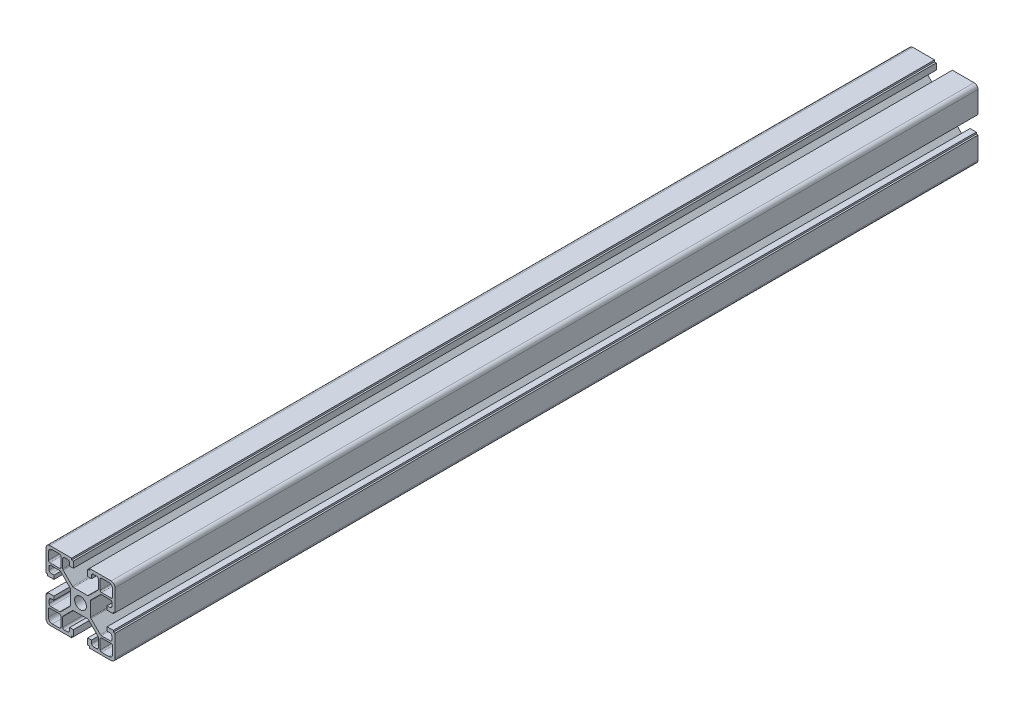
SolidWorks part; units mm, degrees
material "6063-T5"
ref_plane "Front Plane" through (0, 0, 0) normal (0, 0, 1) x (1, 0, 0)
ref_plane "Top Plane" through (0, 0, 0) normal (0, 1, 0) x (1, 0, 0)
ref_plane "Right Plane" through (0, 0, 0) normal (1, 0, 0) x (0, 0, -1)
sketch "Sketch1" plane through (0, 0, 0) normal (0, 0, 1) x (1, 0, 0)
  line L4 (20, 17.75) -> (20, 5.15)
  line L5 (0, -17.7813) -> (0, 18.2) construction
  line L6 (0, 0) -> (38.8613, 0) construction
  line L8 (18.6, 16.35) -> (18.6, 12.2)
  line L10 (11.4, 17.8) -> (11.4, 12.2)
  line L11 (-4.1, 5.85) -> (4.1, 5.85)
  line L14 (5.85, 4.1089) -> (5.85, -4.1089)
  line L17 (12.2, 11.4) -> (17.8, 11.4)
  line L24 (4.15, 19) -> (4.15, 15.4)
  line L25 (4.15, 15.4) -> (6.35, 15.4)
  line L26 (6.35, 15.4) -> (6.35, 16.95)
  line L27 (10.3, 17.2) -> (10.3, 12.0545)
  line L28 (10.0659, 11.489) -> (4.6659, 6.0845)
  line L29 (6.0841, 4.6743) -> (11.4708, 10.0655)
  line L30 (12.0367, 10.3) -> (17.2, 10.3)
  line L31 (18.2, 9.3) -> (18.2, 7.6)
  line L32 (16.95, 6.35) -> (15.4, 6.35)
  line L33 (15.4, 6.35) -> (15.4, 4.15)
  line L34 (15.4, 4.15) -> (19, 4.15)
  line L35 (18.6, 18.6) -> (18.6, -18.6) construction
  line L36 (-18.6, 18.6) -> (18.6, 18.6) construction
  line L37 (-20, 20) -> (20, 20) construction
  line L38 (20, 20) -> (20, -20) construction
  line L40 (7.6, 18.2) -> (9.3, 18.2)
  line L42 (4.15, 19) -> (5.15, 19)
  line L43 (5.15, 19) -> (5.15, 20)
  line L56 (-18.6, 18.6) -> (-18.6, -18.6) construction
  line L57 (-20, 20) -> (-20, -20) construction
  line L60 (5.15, 20) -> (17.75, 20)
  line L91 (-18.6, -18.6) -> (18.6, -18.6) construction
  line L92 (-20, -20) -> (20, -20) construction
  line L93 (12.2, 18.6) -> (16.35, 18.6)
  line L94 (17.9399, 17.9421) -> (20, 20) construction
  line L95 (0, 0) -> (11.4, 11.4094) construction
  line L101 (19, 4.15) -> (19, 5.15)
  line L102 (19, 5.15) -> (20, 5.15)
  line L104 (-5.85, 4.1089) -> (-5.85, -4.1089)
  line L105 (-19, 5.15) -> (-20, 5.15)
  line L106 (-19, 4.15) -> (-19, 5.15)
  line L107 (-12.2, 18.6) -> (-16.35, 18.6)
  line L108 (-5.15, 20) -> (-17.75, 20)
  line L109 (-5.15, 19) -> (-5.15, 20)
  line L110 (-4.15, 19) -> (-5.15, 19)
  line L111 (-7.6, 18.2) -> (-9.3, 18.2)
  line L112 (-15.4, 4.15) -> (-19, 4.15)
  line L113 (-15.4, 6.35) -> (-15.4, 4.15)
  line L114 (-16.95, 6.35) -> (-15.4, 6.35)
  line L115 (-18.2, 9.3) -> (-18.2, 7.6)
  line L116 (-12.0367, 10.3) -> (-17.2, 10.3)
  line L117 (-6.0841, 4.6743) -> (-11.4708, 10.0655)
  line L118 (-10.0659, 11.489) -> (-4.6659, 6.0845)
  line L119 (-10.3, 17.2) -> (-10.3, 12.0545)
  line L120 (-6.35, 15.4) -> (-6.35, 16.95)
  line L121 (-4.15, 15.4) -> (-6.35, 15.4)
  line L122 (-4.15, 19) -> (-4.15, 15.4)
  line L123 (-12.2, 11.4) -> (-17.8, 11.4)
  line L124 (-11.4, 17.8) -> (-11.4, 12.2)
  line L125 (-18.6, 16.35) -> (-18.6, 12.2)
  line L126 (-20, 17.75) -> (-20, 5.15)
  line L127 (-20, -17.75) -> (-20, -5.15)
  line L128 (-18.6, -16.35) -> (-18.6, -12.2)
  line L129 (-11.4, -17.8) -> (-11.4, -12.2)
  line L130 (-12.2, -11.4) -> (-17.8, -11.4)
  line L131 (-4.15, -19) -> (-4.15, -15.4)
  line L132 (-4.15, -15.4) -> (-6.35, -15.4)
  line L133 (-6.35, -15.4) -> (-6.35, -16.95)
  line L134 (-10.3, -17.2) -> (-10.3, -12.0545)
  line L135 (-10.0659, -11.489) -> (-4.6659, -6.0845)
  line L136 (-6.0841, -4.6743) -> (-11.4708, -10.0655)
  line L137 (-12.0367, -10.3) -> (-17.2, -10.3)
  line L138 (-18.2, -9.3) -> (-18.2, -7.6)
  line L139 (-16.95, -6.35) -> (-15.4, -6.35)
  line L140 (-15.4, -6.35) -> (-15.4, -4.15)
  line L141 (-15.4, -4.15) -> (-19, -4.15)
  line L142 (-7.6, -18.2) -> (-9.3, -18.2)
  line L143 (-4.15, -19) -> (-5.15, -19)
  line L144 (-5.15, -19) -> (-5.15, -20)
  line L145 (-5.15, -20) -> (-17.75, -20)
  line L146 (-12.2, -18.6) -> (-16.35, -18.6)
  line L147 (-19, -4.15) -> (-19, -5.15)
  line L148 (-19, -5.15) -> (-20, -5.15)
  line L149 (19, -5.15) -> (20, -5.15)
  line L150 (19, -4.15) -> (19, -5.15)
  line L151 (12.2, -18.6) -> (16.35, -18.6)
  line L152 (5.15, -20) -> (17.75, -20)
  line L153 (5.15, -19) -> (5.15, -20)
  line L154 (4.15, -19) -> (5.15, -19)
  line L155 (7.6, -18.2) -> (9.3, -18.2)
  line L156 (15.4, -4.15) -> (19, -4.15)
  line L157 (15.4, -6.35) -> (15.4, -4.15)
  line L158 (16.95, -6.35) -> (15.4, -6.35)
  line L159 (18.2, -9.3) -> (18.2, -7.6)
  line L160 (12.0367, -10.3) -> (17.2, -10.3)
  line L161 (6.0841, -4.6743) -> (11.4708, -10.0655)
  line L162 (10.0659, -11.489) -> (4.6659, -6.0845)
  line L163 (10.3, -17.2) -> (10.3, -12.0545)
  line L164 (6.35, -15.4) -> (6.35, -16.95)
  line L165 (4.15, -15.4) -> (6.35, -15.4)
  line L166 (4.15, -19) -> (4.15, -15.4)
  line L167 (12.2, -11.4) -> (17.8, -11.4)
  line L168 (-4.1, -5.85) -> (4.1, -5.85)
  line L169 (11.4, -17.8) -> (11.4, -12.2)
  line L170 (18.6, -16.35) -> (18.6, -12.2)
  line L171 (20, -17.75) -> (20, -5.15)
  circle A0 centre (0, 0) radius 3.4
  arc A7 (16.35, 18.6) -> (18.6, 16.35) centre (16.35, 16.35) cw
  arc A8 (20, 17.75) -> (17.75, 20) centre (17.75, 17.75) ccw
  arc A9 (6.35, 16.95) -> (7.6, 18.2) centre (7.6, 16.95) cw
  arc A10 (18.2, 7.6) -> (16.95, 6.35) centre (16.95, 7.6) cw
  arc A11 (17.2, 10.3) -> (18.2, 9.3) centre (17.2, 9.3) cw
  arc A12 (9.3, 18.2) -> (10.3, 17.2) centre (9.3, 17.2) cw
  arc A13 (4.6659, 6.0845) -> (4.1, 5.85) centre (4.1, 6.65) cw
  arc A14 (6.0841, 4.6743) -> (5.85, 4.1089) centre (6.65, 4.1089) ccw
  arc A15 (17.8, 11.4) -> (18.6, 12.2) centre (17.8, 12.2) ccw
  arc A16 (12.2, 18.6) -> (11.4, 17.8) centre (12.2, 17.8) ccw
  arc A17 (11.4, 12.2) -> (12.2, 11.4) centre (12.2, 12.2) ccw
  arc A18 (11.4708, 10.0655) -> (12.0367, 10.3) centre (12.0367, 9.5) cw
  arc A19 (10.3, 12.0545) -> (10.0659, 11.489) centre (9.5, 12.0545) cw
  arc A20 (-10.3, 12.0545) -> (-10.0659, 11.489) centre (-9.5, 12.0545) ccw
  arc A21 (-11.4708, 10.0655) -> (-12.0367, 10.3) centre (-12.0367, 9.5) ccw
  arc A22 (-11.4, 12.2) -> (-12.2, 11.4) centre (-12.2, 12.2) cw
  arc A23 (-12.2, 18.6) -> (-11.4, 17.8) centre (-12.2, 17.8) cw
  arc A24 (-17.8, 11.4) -> (-18.6, 12.2) centre (-17.8, 12.2) cw
  arc A25 (-6.0841, 4.6743) -> (-5.85, 4.1089) centre (-6.65, 4.1089) cw
  arc A26 (-4.6659, 6.0845) -> (-4.1, 5.85) centre (-4.1, 6.65) ccw
  arc A27 (-9.3, 18.2) -> (-10.3, 17.2) centre (-9.3, 17.2) ccw
  arc A28 (-17.2, 10.3) -> (-18.2, 9.3) centre (-17.2, 9.3) ccw
  arc A29 (-18.2, 7.6) -> (-16.95, 6.35) centre (-16.95, 7.6) ccw
  arc A30 (-6.35, 16.95) -> (-7.6, 18.2) centre (-7.6, 16.95) ccw
  arc A31 (-20, 17.75) -> (-17.75, 20) centre (-17.75, 17.75) cw
  arc A32 (-16.35, 18.6) -> (-18.6, 16.35) centre (-16.35, 16.35) ccw
  arc A33 (-16.35, -18.6) -> (-18.6, -16.35) centre (-16.35, -16.35) cw
  arc A34 (-20, -17.75) -> (-17.75, -20) centre (-17.75, -17.75) ccw
  arc A35 (-6.35, -16.95) -> (-7.6, -18.2) centre (-7.6, -16.95) cw
  arc A36 (-18.2, -7.6) -> (-16.95, -6.35) centre (-16.95, -7.6) cw
  arc A37 (-17.2, -10.3) -> (-18.2, -9.3) centre (-17.2, -9.3) cw
  arc A38 (-9.3, -18.2) -> (-10.3, -17.2) centre (-9.3, -17.2) cw
  arc A39 (-4.6659, -6.0845) -> (-4.1, -5.85) centre (-4.1, -6.65) cw
  arc A40 (-6.0841, -4.6743) -> (-5.85, -4.1089) centre (-6.65, -4.1089) ccw
  arc A41 (-17.8, -11.4) -> (-18.6, -12.2) centre (-17.8, -12.2) ccw
  arc A42 (-12.2, -18.6) -> (-11.4, -17.8) centre (-12.2, -17.8) ccw
  arc A43 (-11.4, -12.2) -> (-12.2, -11.4) centre (-12.2, -12.2) ccw
  arc A44 (-11.4708, -10.0655) -> (-12.0367, -10.3) centre (-12.0367, -9.5) cw
  arc A45 (-10.3, -12.0545) -> (-10.0659, -11.489) centre (-9.5, -12.0545) cw
  arc A46 (10.3, -12.0545) -> (10.0659, -11.489) centre (9.5, -12.0545) ccw
  arc A47 (11.4708, -10.0655) -> (12.0367, -10.3) centre (12.0367, -9.5) ccw
  arc A48 (11.4, -12.2) -> (12.2, -11.4) centre (12.2, -12.2) cw
  arc A49 (12.2, -18.6) -> (11.4, -17.8) centre (12.2, -17.8) cw
  arc A50 (17.8, -11.4) -> (18.6, -12.2) centre (17.8, -12.2) cw
  arc A51 (6.0841, -4.6743) -> (5.85, -4.1089) centre (6.65, -4.1089) cw
  arc A52 (4.6659, -6.0845) -> (4.1, -5.85) centre (4.1, -6.65) ccw
  arc A53 (9.3, -18.2) -> (10.3, -17.2) centre (9.3, -17.2) ccw
  arc A54 (17.2, -10.3) -> (18.2, -9.3) centre (17.2, -9.3) ccw
  arc A55 (18.2, -7.6) -> (16.95, -6.35) centre (16.95, -7.6) ccw
  arc A56 (6.35, -16.95) -> (7.6, -18.2) centre (7.6, -16.95) ccw
  arc A57 (20, -17.75) -> (17.75, -20) centre (17.75, -17.75) cw
  arc A58 (16.35, -18.6) -> (18.6, -16.35) centre (16.35, -16.35) ccw
  point P0 (0, 0)
  point P16 (-5.85, 0)
  point P66 (0, 5.85)
  point P120 (5.85, 0)
  point P218 (0, -5.85)
  dimension "D5" = 6.8
  dimension "D6" = 1.4
  dimension "D15" = 5.85
  dimension "D44" = 2.25
  dimension "D25" = 1.25
  dimension "D26" = 1
  dimension "D27" = 0.8
  dimension "D7" = 1.1
  dimension "D8" = 1.1
  dimension "D9" = 1.8
  dimension "D10" = 2.2
  dimension "D11" = 4.6
  dimension "D12" = 1.8
  dimension "D13" = 2.2
  dimension "D14" = 5.85
  dimension "D16" = 1.4
  dimension "D17" = 4.15
  dimension "D18" = 1
  dimension "D19" = 1
  dimension "D20" = 10.3
  dimension "D21" = 4.15
  dimension "D22" = 2
  dimension "D23" = 45.024
  dimension "D24" = 1
  dimension "D41" = 10.3
  dimension "D60" = 14.15
  dimension "D73" = 1
  dimension "D74" = 1
  dimension "D82" = 14.15
  dimension "D3" = 4.6
extrude "Boss-Extrude1" add sketch "Sketch1" along normal blind 500
